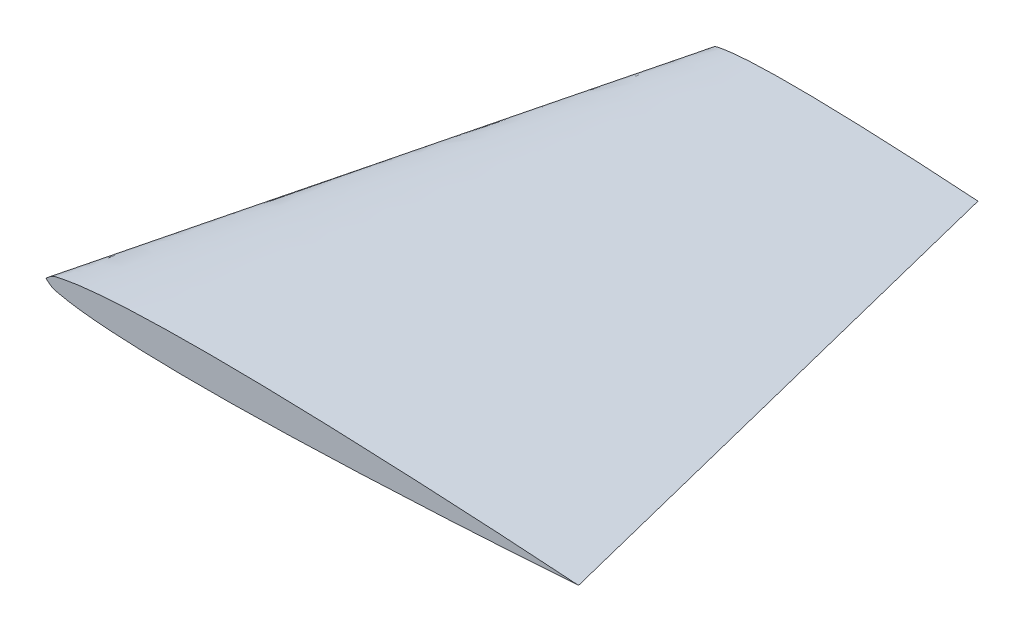
SolidWorks part; units mm, degrees
ref_plane "Front Plane" through (0, 0, 0) normal (0, 0, 1) x (1, 0, 0)
ref_plane "Top Plane" through (0, 0, 0) normal (0, 1, 0) x (1, 0, 0)
ref_plane "Right Plane" through (0, 0, 0) normal (1, 0, 0) x (0, 0, -1)
curve "Curve2"
  spline degree 3 poles (25.4, 0.016, 0) (24.9767, 0.0451, 0) (24.1302, 0.1034, 0) (22.437, 0.2117, 0) (20.3205, 0.3361, 0) (17.7804, 0.4681, 0) (15.2404, 0.5832, 0) (12.7004, 0.6768, 0) (10.1604, 0.7436, 0) (8.0434, 0.7669, 0) (6.3499, 0.7577, 0) (5.0796, 0.7326, 0) (3.8092, 0.6843, 0) (2.7503, 0.6171, 0) (1.9043, 0.5359, 0) (1.2655, 0.4592, 0) (0.7416, 0.3537, 0) (0.2823, 0.2604, 0) (0.0998, 0.092, 0) (0, 0, 0) knots 0 0 0 0 0.049849 0.099686 0.199326 0.298929 0.398498 0.498033 0.597534 0.697007 0.746742 0.796487 0.846259 0.896103 0.921086 0.946159 0.971462 0.984401 1 1 1 1
sketch "Sketch3" plane through (0, 0, 0) normal (0, 0, 1) x (1, 0, 0)
  line L0 (0, 0) -> (25.4, 0.016) construction
  spline S0 degree 3 poles (406.4258, 2972.3876) (144.7213, -29.1509) (84.7185, -3.7726) (22.437, 0.2117) (20.3205, 0.3361) (17.7804, 0.4681) (15.2404, 0.5832) (12.7004, 0.6768) (10.1604, 0.7436) (8.0434, 0.7669) (6.3499, 0.7577) (5.0796, 0.7326) (3.8092, 0.6843) (2.7503, 0.6171) (1.9043, 0.5359) (1.2655, 0.4592) (0.7416, 0.3537) (-5.3363, -0.8815) (24.1328, -70.989) (-1383.0423, 2661.4272) knots -7.132594 -7.132594 -7.132594 -7.132594 0.049849 0.099686 0.199326 0.298929 0.398498 0.498033 0.597534 0.697007 0.746742 0.796487 0.846259 0.896103 0.921086 0.946159 0.971462 0.984401 1.658608 1.658608 1.658608 1.658608 only from (25.4, 0.016) to (0, 0) construction
  spline S1 degree 3 poles (25.4, 0.016) (24.9767, 0.0451) (24.1302, 0.1034) (22.437, 0.2117) (20.3205, 0.3361) (17.7804, 0.4681) (15.2404, 0.5832) (12.7004, 0.6768) (10.1604, 0.7436) (8.0434, 0.7669) (6.3499, 0.7577) (5.0796, 0.7326) (3.8092, 0.6843) (2.7503, 0.6171) (1.9043, 0.5359) (1.2655, 0.4592) (0.7416, 0.3537) (0.2823, 0.2604) (0.0998, 0.092) (0, 0) knots 0 0 0 0 0.049849 0.099686 0.199326 0.298929 0.398498 0.498033 0.597534 0.697007 0.746742 0.796487 0.846259 0.896103 0.921086 0.946159 0.971462 0.984401 1 1 1 1
  spline S2 degree 3 poles (25.4, 0.016) (24.9767, -0.0137) (24.1303, -0.073) (22.4372, -0.1834) (20.3209, -0.3105) (17.781, -0.4457) (15.2412, -0.564) (12.7013, -0.6608) (10.1613, -0.7308) (8.0443, -0.7567) (6.3508, -0.7497) (5.0806, -0.7262) (3.8101, -0.6795) (2.751, -0.6137) (1.905, -0.5335) (1.2661, -0.4576) (0.742, -0.3528) (0.2826, -0.26) (0.0999, -0.0919) (0, 0) knots 0 0 0 0 0.049849 0.099686 0.199326 0.298929 0.398498 0.498033 0.597534 0.697007 0.746742 0.796487 0.846259 0.896103 0.921086 0.946159 0.971462 0.984401 1 1 1 1
ref_plane "Plane1" through (0, 0, -25.4) normal (0, 0, 1) x (1, 0, 0)
sketch "Sketch4" plane through (0, 0, -25.4) normal (0, 0, 1) x (1, 0, 0)
  spline S2 degree 3 poles (19.05, 0.012) (18.8384, -0.0028) (18.4151, -0.0325) (17.1456, -0.1153) (15.6641, -0.1991) (13.9706, -0.278) (12.7006, -0.3264) (11.4307, -0.3614) (10.3722, -0.3744) (9.5254, -0.3708) (8.8903, -0.3591) (8.255, -0.3357) (7.7255, -0.3028) (7.3025, -0.2627) (6.9831, -0.2248) (6.721, -0.1724) (6.4913, -0.126) (6.3999, -0.0419) (6.35, 0.004) knots 0 0 0 0 0.049849 0.099686 0.298929 0.398498 0.498033 0.597534 0.697007 0.746742 0.796487 0.846259 0.896103 0.921086 0.946159 0.971462 0.984401 1 1 1 1
  spline S3 degree 3 poles (19.05, 0.012) (18.8383, 0.0266) (18.4151, 0.0557) (17.1455, 0.1369) (15.6638, 0.2189) (13.9702, 0.2956) (12.7002, 0.3424) (11.4302, 0.3758) (10.3717, 0.3874) (9.5249, 0.3828) (8.8898, 0.3703) (8.2546, 0.3461) (7.7251, 0.3126) (7.3022, 0.2719) (6.9828, 0.2336) (6.7208, 0.1809) (6.4911, 0.1342) (6.3999, 0.05) (6.35, 0.004) knots 0 0 0 0 0.049849 0.099686 0.298929 0.398498 0.498033 0.597534 0.697007 0.746742 0.796487 0.846259 0.896103 0.921086 0.946159 0.971462 0.984401 1 1 1 1
loft "Loft1" add profiles "Sketch3", "Sketch4"
